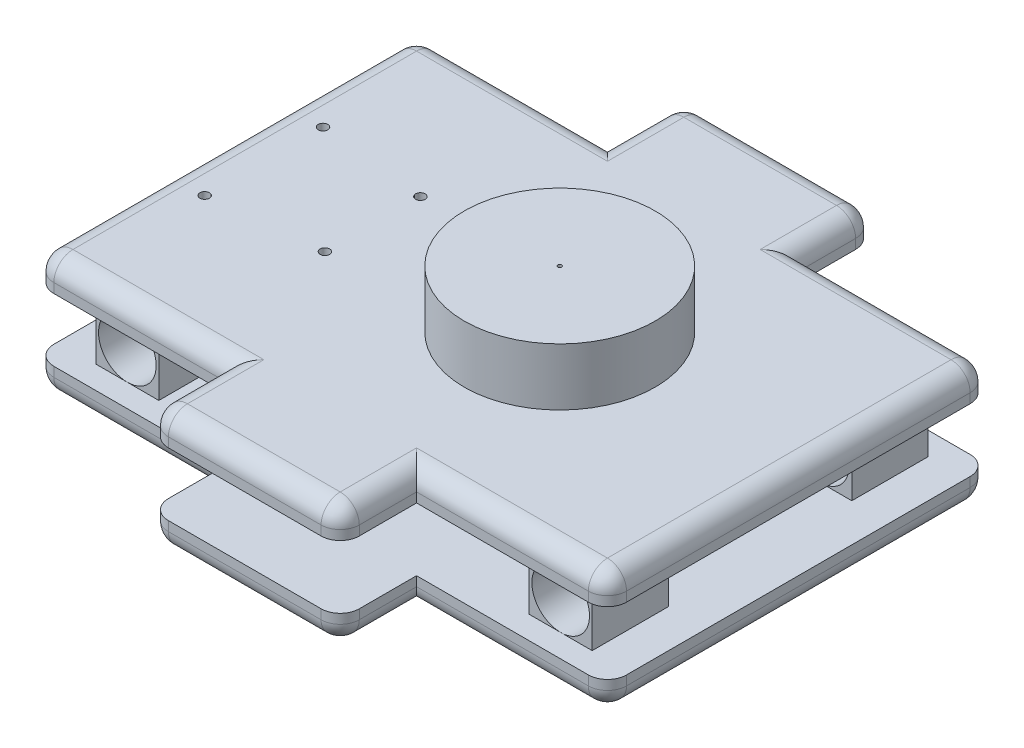
SolidWorks part; units mm, degrees
ref_plane "Front Plane" through (0, 0, 0) normal (0, 0, 1) x (1, 0, 0)
ref_plane "Top Plane" through (0, 0, 0) normal (0, 1, 0) x (1, 0, 0)
ref_plane "Right Plane" through (0, 0, 0) normal (1, 0, 0) x (0, 0, -1)
sketch "Sketch1" plane through (0, 0, 0) normal (0, 1, 0) x (1, 0, 0)
  line L1 (0, 0) -> (300, 0)
  line L2 (0, 0) -> (0, -200)
  line L3 (0, -200) -> (300, -200)
  line L4 (300, 0) -> (300, -200)
extrude "Boss-Extrude1" add sketch "Sketch1" along normal blind 15
sketch "Sketch3" plane through (0, 15, 0) normal (0, 1, 0) x (1, 0, 0)
  line L5 (280, -188) -> (247, -188)
  line L6 (280, -188) -> (280, -148)
  line L7 (280, -148) -> (247, -148)
  line L8 (247, -188) -> (247, -148)
  line L11 (280, -12) -> (247, -12)
  line L12 (280, -12) -> (280, -52)
  line L13 (280, -52) -> (247, -52)
  line L14 (247, -12) -> (247, -52)
  line L17 (20, -12) -> (53, -12)
  line L18 (20, -12) -> (20, -52)
  line L19 (20, -52) -> (53, -52)
  line L20 (53, -12) -> (53, -52)
  line L21 (20, -148) -> (53, -148)
  line L22 (20, -148) -> (20, -188)
  line L23 (20, -188) -> (53, -188)
  line L24 (53, -148) -> (53, -188)
extrude "Boss-Extrude2" add sketch "Sketch3" along normal blind 33
sketch "Sketch4" plane through (0, 0, 188) normal (0, 0, 1) x (1, 0, 0)
  circle A0 centre (36.5, 30.1) radius 15.1
  circle A1 centre (263.5, 30.1) radius 15.1
extrude "Cut-Extrude1" cut sketch "Sketch4" against normal blind 222
sketch "Sketch5" plane through (0, 48, 0) normal (0, 1, 0) x (1, 0, 0)
  line L1 (0, 0) -> (300, 0)
  line L2 (0, 0) -> (0, -200)
  line L3 (0, -200) -> (300, -200)
  line L4 (300, 0) -> (300, -200)
extrude "Boss-Extrude3" add sketch "Sketch5" along normal blind 15
sketch "Sketch6" plane through (0, 0, 0) normal (0, 0, -1) x (-1, 0, 0)
  line L1 (-300, 63) -> (0, 63) construction
  line L3 (-300, 48) -> (0, 48) construction
  line L4 (-200, 63) -> (-100, 63)
  line L5 (-200, 63) -> (-200, 48)
  line L6 (-200, 48) -> (-100, 48)
  line L7 (-100, 63) -> (-100, 48)
  line L8 (-300, 15) -> (0, 15) construction
  line L9 (-200, 15) -> (-100, 15)
  line L10 (-200, 15) -> (-200, 0)
  line L11 (-200, 0) -> (-100, 0)
  line L12 (-100, 15) -> (-100, 0)
  line L13 (-300, 0) -> (0, 0) construction
extrude "Boss-Extrude4" add sketch "Sketch6" along normal blind 40 and the other way blind 240
fillet "Fillet1" radius 10 16 edges at (300, 55.5, 0) (300, 7.5, 0) (0, 55.5, 0) (0, 7.5, 0) (0, 55.5, 200) (0, 7.5, 200) (300, 55.5, 200) (300, 7.5, 200) (200, 7.5, 240) (200, 55.5, 240) (100, 7.5, 240) (100, 55.5, 240) (100, 7.5, -40) (200, 7.5, -40) (200, 55.5, -40) (100, 55.5, -40)
sketch "Sketch11" plane through (0, 15, 0) normal (0, 1, 0) x (1, 0, 0)
  line L0 (0, -100) -> (0, -82.3)
  line L1 (0, -10) -> (0, -190) construction
  line L2 (0, -100) -> (0, -117.7)
  line L4 (0, -82.3) -> (10, -82.3)
  line L5 (0, -82.3) -> (0, -117.7)
  line L6 (0, -117.7) -> (10, -117.7)
  line L7 (10, -82.3) -> (10, -117.7)
  line M17 (0, -10) -> (0, -190)
extrude "Boss-Extrude7" add sketch "Sketch11" along normal blind 34 contours L7 L4 L6 M17
fillet "Fillet2" radius 10 20 edges at (297.0711, 63, 2.9289) (300, 63, 100) (297.0711, 63, 197.0711) (245, 63, 200) (200, 63, 215) (197.0711, 63, 237.0711) (150, 63, 240) (102.9289, 63, 237.0711) (100, 63, 215) (55, 63, 200) (2.9289, 63, 197.0711) (0, 63, 100) (2.9289, 63, 2.9289) (55, 63, 0) (100, 63, -15) (102.9289, 63, -37.0711) (197.0711, 63, -37.0711) (200, 63, -15) (150, 63, -40) (245, 63, 0)
fillet "Fillet3" radius 10 20 edges at (297.0711, 0, 197.0711) (245, 0, 200) (200, 0, 215) (197.0711, 0, 237.0711) (150, 0, 240) (102.9289, 0, 237.0711) (100, 0, 215) (55, 0, 200) (2.9289, 0, 197.0711) (0, 0, 100) (2.9289, 0, 2.9289) (55, 0, 0) (100, 0, -15) (102.9289, 0, -37.0711) (150, 0, -40) (197.0711, 0, -37.0711) (200, 0, -15) (245, 0, 0) (297.0711, 0, 2.9289) (300, 0, 100)
sketch "Sketch12" plane through (0, 0, 0) normal (-1, 0, 0) x (0, 0, 1)
  circle A0 centre (100, 31.5) radius 1
extrude "Cut-Extrude4" cut sketch "Sketch12" against normal blind 1
sketch "Sketch13" plane through (0, 63, 0) normal (0, 1, 0) x (1, 0, 0)
  circle A0 centre (150, -100) radius 2.5
extrude "Cut-Extrude5" cut sketch "Sketch13" against normal blind 27
sketch "Sketch14" plane through (0, 63, 0) normal (0, 1, 0) x (1, 0, 0)
  circle A9 centre (20, -131) radius 2.5
  circle A10 centre (20, -69) radius 2.5
  circle A11 centre (77, -75) radius 2.5
  circle A12 centre (77, -125) radius 2.5
extrude "Cut-Extrude6" cut sketch "Sketch14" against normal blind 32
sketch "Sketch15" plane through (0, 63, 0) normal (0, 1, 0) x (1, 0, 0)
  circle A1 centre (175, -100) radius 50
extrude "Boss-Extrude9" add sketch "Sketch15" along normal blind 30 contours A1
sketch "Sketch16" plane through (0, 93, 0) normal (0, 1, 0) x (1, 0, 0)
  circle A0 centre (175, -100) radius 1
extrude "Cut-Extrude7" cut sketch "Sketch16" against normal blind 63
